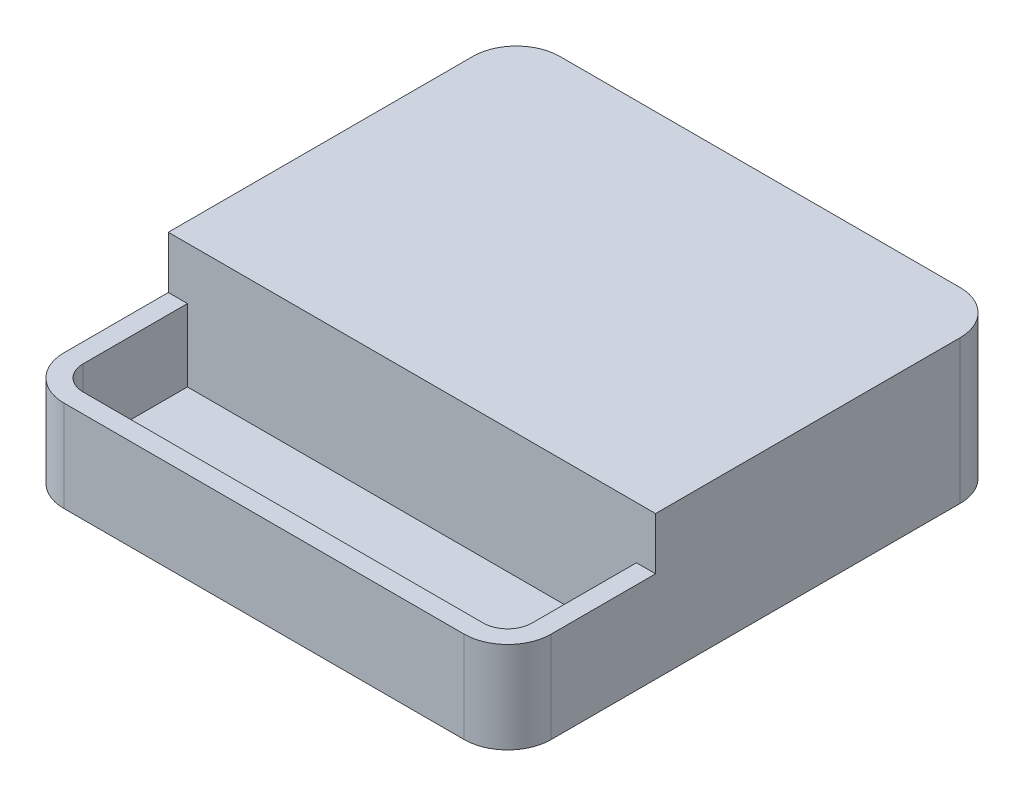
SolidWorks part; units mm, degrees
ref_plane "前视基准面" through (0, 0, 0) normal (0, 0, 1) x (1, 0, 0)
ref_plane "上视基准面" through (0, 0, 0) normal (0, 1, 0) x (1, 0, 0)
ref_plane "右视基准面" through (0, 0, 0) normal (1, 0, 0) x (0, 0, -1)
other "Configuration Table"
sketch "草图1" plane through (0, 0, 0) normal (0, 1, 0) x (1, 0, 0)
  line L0 (-23, 28.5) -> (23, 28.5)
  line L1 (-28, 23.5) -> (-28, -23.5)
  line L2 (-23, -28.5) -> (23, -28.5)
  line L3 (28, 23.5) -> (28, -23.5)
  line L4 (0, 0) -> (0, 11.9303) construction
  line L5 (0, 0) -> (17.3862, 0) construction
  arc A0 (-23, 28.5) -> (-28, 23.5) centre (-23, 23.5) ccw
  arc A1 (23, 28.5) -> (28, 23.5) centre (23, 23.5) cw
  arc A2 (-28, -23.5) -> (-23, -28.5) centre (-23, -23.5) ccw
  arc A3 (28, -23.5) -> (23, -28.5) centre (23, -23.5) cw
  dimension "D3" = 5
  dimension "D1" = 56
  dimension "D2" = 57
extrude "凸台-拉伸1" add sketch "草图1" along normal blind 16.5
sketch "草图2" plane through (0, 16.5, 0) normal (0, 1, 0) x (1, 0, 0)
  line L0 (-28, 23.5) -> (-28, -23.5) construction
  line L1 (-28, -11.5) -> (28, -11.5)
  line L2 (-28, -11.5) -> (-28, -28.5)
  line L3 (-28, -28.5) -> (28, -28.5)
  line L4 (28, -11.5) -> (28, -28.5)
  line L5 (28, -23.5) -> (28, 23.5) construction
  line L6 (-23, -28.5) -> (23, -28.5) construction
  dimension "D1" = 17
extrude "切除-拉伸1" cut sketch "草图2" against normal blind 6
sketch "草图3" plane through (0, 10.5, 0) normal (0, 1, 0) x (1, 0, 0)
  line L0 (-25.8, -11.5) -> (25.8, -11.5)
  line L1 (25.8, -11.5) -> (25.8, -23.5)
  line L2 (-25.8, -11.5) -> (-25.8, -23.5)
  line L3 (-23, -26.3) -> (23, -26.3)
  line L4 (-23, -28.5) -> (23, -28.5) construction
  line L5 (28, -23.5) -> (28, -11.5) construction
  line L6 (-28, -11.5) -> (-28, -23.5) construction
  line L7 (28, -11.5) -> (-28, -11.5) construction
  arc A0 (-25.8, -23.5) -> (-23, -26.3) centre (-23, -23.5) ccw
  arc A1 (23, -26.3) -> (25.8, -23.5) centre (23, -23.5) ccw
  dimension "D1" = 2.2
  dimension "D2" = 2.2
  dimension "D3" = 2.2
extrude "切除-拉伸2" cut sketch "草图3" against normal offset from surface (8.3 mm away) 2.2 up to face at (0, 0, 0)
sketch "草图4" plane through (0, 0, 0) normal (0, -1, 0) x (1, 0, 0)
  line L0 (-23, 28.5) -> (23, 28.5) construction
  line L1 (-21, 23.5) -> (21, 23.5) construction
  line L2 (-21, 23.5) -> (-21, -23.5) construction
  line L3 (-21, -23.5) -> (21, -23.5) construction
  line L4 (21, 23.5) -> (21, -23.5) construction
  line L5 (23, -28.5) -> (-23, -28.5) construction
  line L6 (28, 23.5) -> (28, -23.5) construction
  line L7 (-28, -23.5) -> (-28, 23.5) construction
  circle A0 centre (0, 0) radius 7
  circle A1 centre (-21, 23.5) radius 0.5
  circle A2 centre (21, 23.5) radius 0.5
  circle A3 centre (-21, -23.5) radius 0.5
  circle A4 centre (21, -23.5) radius 0.5
  dimension "D1" = 14
  dimension "D6" = 1
  dimension "D2" = 5
  dimension "D3" = 5
  dimension "D4" = 7
  dimension "D5" = 7
extrude "凸台-拉伸2" add sketch "草图4" along normal blind 1
sketch "草图5" plane through (0, -1, 0) normal (0, -1, 0) x (1, 0, 0)
  circle A0 centre (0, 0) radius 4
  dimension "D1" = 8
extrude "凸台-拉伸3" add sketch "草图5" along normal blind 4.5
sketch "草图6" plane through (0, -5.5, 0) normal (0, -1, 0) x (1, 0, 0)
  circle A0 centre (0, 0) radius 2.8
  dimension "D1" = 5.6
extrude "凸台-拉伸4" add sketch "草图6" along normal blind 4
sketch "草图7" plane through (0, -9.5, 0) normal (0, -1, 0) x (1, 0, 0)
  circle A0 centre (0, 0) radius 1.875
  dimension "D1" = 3.75
extrude "凸台-拉伸5" add sketch "草图7" along normal blind 3.5
